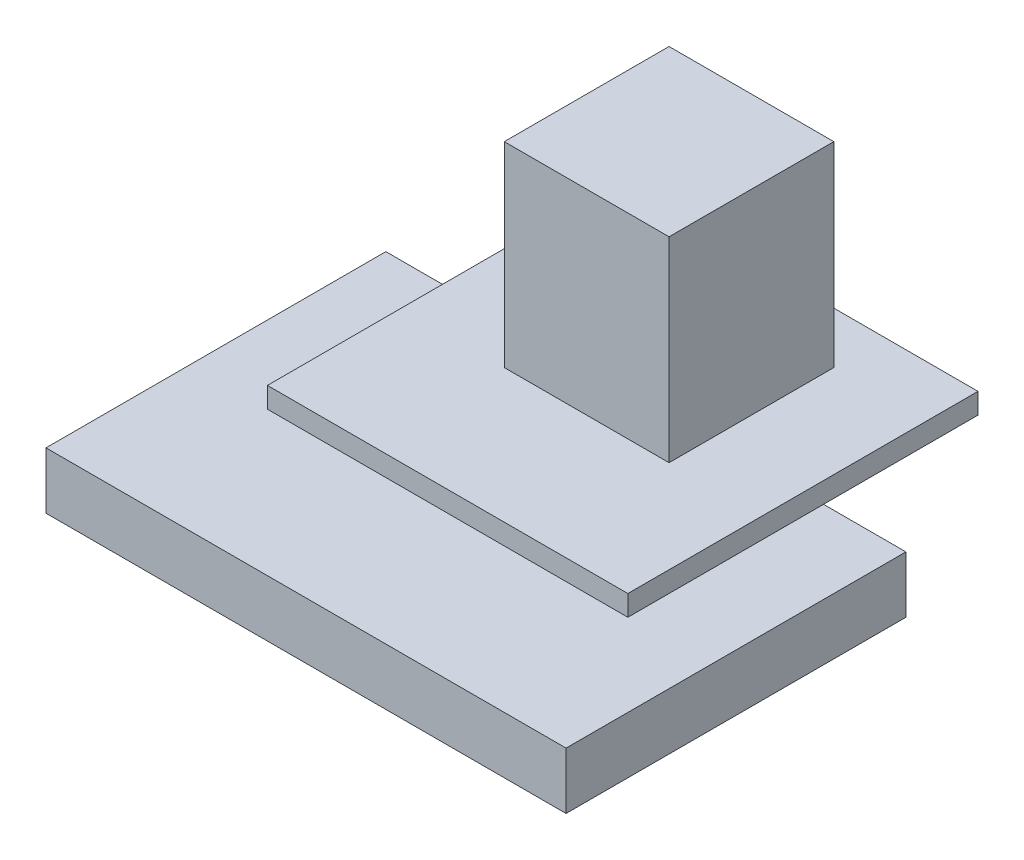
SolidWorks part; units mm, degrees
ref_plane "Front Plane" through (0, 0, 0) normal (0, 0, 1) x (1, 0, 0)
ref_plane "Top Plane" through (0, 0, 0) normal (0, 1, 0) x (1, 0, 0)
ref_plane "Right Plane" through (0, 0, 0) normal (1, 0, 0) x (0, 0, -1)
sketch "Sketch1" plane through (0, 0, 0) normal (0, 1, 0) x (1, 0, 0)
  line L1 (0, 0) -> (50.5, 0)
  line L2 (0, 0) -> (0, 33)
  line L3 (0, 33) -> (50.5, 33)
  line L4 (50.5, 0) -> (50.5, 33)
  dimension "D1" = 33
  dimension "D2" = 50.5
extrude "Boss-Extrude1" add sketch "Sketch1" along normal blind 5.5
sketch "Sketch2" plane through (0, 5.5, 0) normal (0, 1, 0) x (1, 0, 0)
  line L1 (7.5, 14) -> (42.5, 14)
  line L2 (7.5, 14) -> (7.5, 48)
  line L3 (7.5, 48) -> (42.5, 48)
  line L4 (42.5, 14) -> (42.5, 48)
  line L6 (50.5, 0) -> (50.5, 33) construction
  line L7 (50.5, 33) -> (0, 33) construction
  dimension "D1" = 34
  dimension "D2" = 35
  dimension "D3" = 8
  dimension "D4" = 19
extrude "Boss-Extrude2" add sketch "Sketch2" along normal blind 2
sketch "Sketch3" plane through (0, 7.5, 0) normal (0, 1, 0) x (1, 0, 0)
  line L0 (42.5, 14) -> (42.5, 48) construction
  line L1 (17.5, 27) -> (33.5, 27)
  line L2 (17.5, 27) -> (17.5, 43)
  line L3 (17.5, 43) -> (33.5, 43)
  line L4 (33.5, 27) -> (33.5, 43)
  line L5 (42.5, 48) -> (7.5, 48) construction
  dimension "D1" = 16
  dimension "D2" = 16
  dimension "D3" = 9
  dimension "D4" = 5
extrude "Boss-Extrude3" add sketch "Sketch3" along normal blind 19
